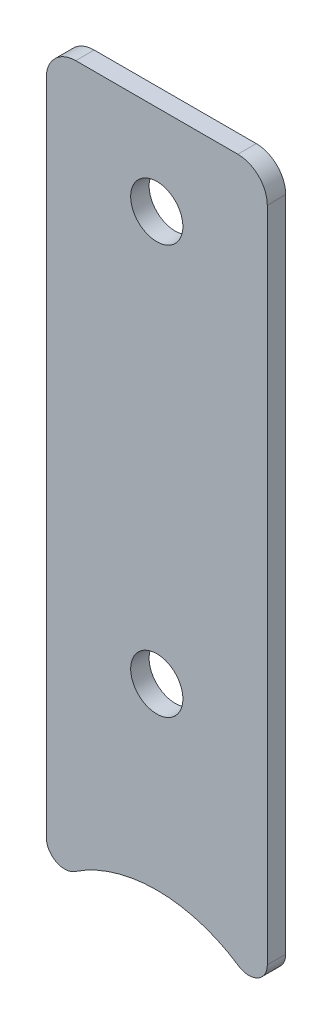
SolidWorks part; units mm, degrees
material "ASTM A36 Steel"
ref_plane "X-Y Datum" through (0, 0, 0) normal (0, 0, 1) x (1, 0, 0)
ref_plane "X-Z Datum" through (0, 0, 0) normal (0, 1, 0) x (1, 0, 0)
ref_plane "Y-Z Datum" through (0, 0, 0) normal (1, 0, 0) x (0, 0, -1)
sketch "Sketch1" plane through (0, 0, 0) normal (0, 0, 1) x (1, 0, 0)
  line L0 (0, 17.6276) -> (0, -17.6276)
  line L1 (-9.525, 25.4) -> (9.525, 25.4)
  line L2 (-9.525, 25.4) -> (-9.525, -25.4)
  line L3 (-9.525, -25.4) -> (9.525, -25.4)
  line L4 (9.525, 25.4) -> (9.525, -25.4)
  line L5 (-9.525, 25.4) -> (9.525, -25.4) construction
  line L6 (-9.525, -25.4) -> (9.525, 25.4) construction
  point P0 (0, 0)
  point P9 (0, 0)
  point P10 (0, 17.6276)
  point P11 (0, -17.6276)
  dimension "D1" = 35.2552
  dimension "D2" = 19.05
  dimension "D3" = 50.8
extrude "Boss-Extrude1" add sketch "Sketch1" along normal blind 1.5875
hole_wizard "M4 Clearance Hole1" positions "Sketch2" profile "Sketch3" hole size "M4" standard "ANSI Metric" end condition through all
sketch "Sketch2" plane through (0, 0, 1.5875) normal (0, 0, 1) x (1, 0, 0)
  point P0 (0, 17.6276)
  point P3 (0, -17.6276)
sketch "Sketch3" plane through (0, 17.6276, 1.5875) normal (1, 0, 0) x (0, -1, 0)
  line L0 (0, 0) -> (0, 1.5875)
  line L1 (0, 1.5875) -> (2.25, 1.5875)
  line L2 (2.25, 1.5875) -> (2.25, 0)
  line L5 (2.25, 0) -> (0, 0)
  line L11 (0, -6.35) -> (0, 107.95) construction
  dimension "Thru Hole Dia." = 4.5
  dimension "Thru Hole Depth" = 1.5875
sketch "Sketch4" plane through (0, 0, 1.5875) normal (0, 0, 1) x (1, 0, 0)
  line L0 (9.525, 25.4) -> (9.525, -25.4) construction
  line L1 (-9.525, -25.4) -> (9.525, -25.4)
  line L2 (-9.525, -25.4) -> (-9.525, -33.02)
  line L3 (-9.525, -33.02) -> (9.525, -33.02)
  line L4 (9.525, -25.4) -> (9.525, -33.02)
  dimension "D1" = 7.62
extrude "Boss-Extrude2" add sketch "Sketch4" against normal blind 1.5875
fillet "Fillet1" radius 2.54 2 edges at (-9.525, 25.4, 0.7937) (9.525, 25.4, 0.7937)
sketch "Sketch5" plane through (0, 0, 1.5875) normal (0, 0, 1) x (1, 0, 0)
  line L0 (-9.525, -33.02) -> (-9.525, -37.3197)
  line L1 (9.525, -33.02) -> (9.525, -37.3197)
  circle A0 centre (0, -45.72) radius 12.7
  line M7 (-9.525, -33.02) -> (9.525, -33.02)
  dimension "D1" = 25.4
  dimension "D2" = 45.72
extrude "Boss-Extrude3" add sketch "Sketch5" against normal blind 1.5875 contours A0 L0 M7 | A0 L1 M7
fillet "Fillet2" radius 1.5875 2 edges at (9.525, -37.3197, 0.7937) (-9.525, -37.3197, 0.7937)
